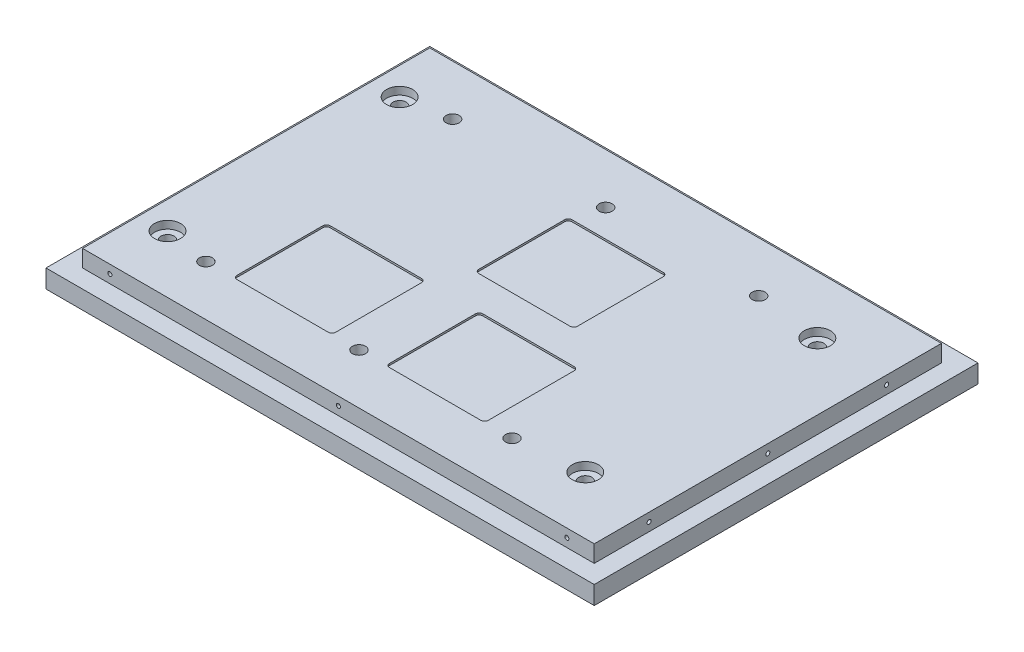
SolidWorks part; units mm, degrees
ref_plane "Front Plane" through (0, 0, 0) normal (0, 0, 1) x (1, 0, 0)
ref_plane "Top Plane" through (0, 0, 0) normal (0, 1, 0) x (1, 0, 0)
ref_plane "Right Plane" through (0, 0, 0) normal (1, 0, 0) x (0, 0, -1)
sketch "Sketch1" plane through (0, 0, 0) normal (0, 1, 0) x (1, 0, 0)
  line L1 (-172.8643, 102.5126) -> (127.1357, 102.5126)
  line L2 (-172.8643, 102.5126) -> (-172.8643, -107.4874)
  line L3 (-172.8643, -107.4874) -> (127.1357, -107.4874)
  line L4 (127.1357, 102.5126) -> (127.1357, -107.4874)
  dimension "D1" = 210
  dimension "D2" = 300
extrude "Boss-Extrude1" add sketch "Sketch1" along normal blind 10
sketch "Sketch2" plane through (0, 10, 0) normal (0, 1, 0) x (1, 0, 0)
  line L0 (-172.8643, 102.5126) -> (-172.8643, -107.4874) construction
  line L1 (-162.8643, 92.5126) -> (117.1357, 92.5126)
  line L2 (-162.8643, 92.5126) -> (-162.8643, -97.4874)
  line L3 (-162.8643, -97.4874) -> (117.1357, -97.4874)
  line L4 (117.1357, 92.5126) -> (117.1357, -97.4874)
  line L5 (127.1357, 102.5126) -> (-172.8643, 102.5126) construction
  line L6 (-172.8643, -107.4874) -> (127.1357, -107.4874) construction
  line L7 (127.1357, -107.4874) -> (127.1357, 102.5126) construction
  dimension "D1" = 10
  dimension "D2" = 10
  dimension "D3" = 10
  dimension "D4" = 10
extrude "Boss-Extrude2" add sketch "Sketch2" along normal blind 9.28
sketch "Sketch3" plane through (0, 19.28, 0) normal (0, 1, 0) x (1, 0, 0)
  line L0 (-162.8643, 92.5126) -> (-162.8643, -97.4874) construction
  line L1 (-122.8643, 65.0126) -> (44.6357, 65.0126)
  line L2 (-122.8643, 65.0126) -> (-122.8643, -69.9874)
  line L3 (-122.8643, -69.9874) -> (44.6357, -69.9874)
  line L4 (44.6357, 65.0126) -> (44.6357, -69.9874)
  line L5 (-39.1143, 65.0126) -> (-39.1143, -69.9874)
  line L6 (-122.8643, -2.4874) -> (44.6357, -2.4874)
  line L8 (-115.3772, -23.5809) -> (-65.3772, -23.5809)
  line L9 (-115.3772, -23.5809) -> (-115.3772, 26.4191)
  line L10 (-115.3772, 26.4191) -> (-65.3772, 26.4191)
  line L11 (-65.3772, -23.5809) -> (-65.3772, 26.4191)
  line L12 (-18.206, 15.3076) -> (31.794, 15.3076)
  line L13 (-18.206, 15.3076) -> (-18.206, 65.3076)
  line L14 (-18.206, 65.3076) -> (31.794, 65.3076)
  line L15 (31.794, 15.3076) -> (31.794, 65.3076)
  circle A0 centre (-122.8643, 65.0126) radius 3.57
  circle A1 centre (-39.1143, 65.0126) radius 3.57
  circle A2 centre (44.6357, 65.0126) radius 3.57
  circle A3 centre (44.6357, -69.9874) radius 3.57
  circle A4 centre (-39.1143, -69.9874) radius 3.57
  circle A5 centre (-122.8643, -69.9874) radius 3.57
  point P4 (-122.8643, -2.4874)
  point P7 (-162.8643, -2.4874)
  dimension "D5" = 7.14
  dimension "D6" = 7.14
  dimension "D1" = 167.5
  dimension "D2" = 135
  dimension "D3" = 0
  dimension "D4" = 40
  dimension "D7" = 50
  dimension "D8" = 50
  dimension "D9" = 50
  dimension "D10" = 50
extrude "1/4-20 clearance holes" cut sketch "Sketch3" against normal up to next contours A0 | A1 | A2 | A3 | A4 | A5
sketch "Sketch4" plane through (0, 0, 0) normal (0, -1, 0) x (1, 0, 0)
  line L0 (-39.1143, 69.9874) -> (-39.1143, -65.0126)
  line L1 (-122.8643, 69.9874) -> (44.6357, 69.9874)
  line L2 (-122.8643, 69.9874) -> (-122.8643, -65.0126)
  line L3 (-122.8643, -65.0126) -> (44.6357, -65.0126)
  line L4 (44.6357, 69.9874) -> (44.6357, -65.0126)
  line L5 (-122.8643, 2.4874) -> (44.6357, 2.4874)
  circle A0 centre (-122.8643, 69.9874) radius 7.5
  circle A1 centre (-39.1143, 69.9874) radius 7.5
  circle A2 centre (44.6357, 69.9874) radius 7.5
  circle A3 centre (44.6357, -65.0126) radius 7.5
  circle A4 centre (-39.1143, -65.0126) radius 7.5
  circle A5 centre (-122.8643, -65.0126) radius 7.5
  dimension "D1" = 15
  dimension "D2" = 15
extrude "Cut-Extrude2" cut sketch "Sketch4" against normal blind 10 contours A0 | A5 | A4 | A3 | A2 | A1
sketch "Sketch5" plane through (0, 0, 97.4874) normal (0, 0, 1) x (1, 0, 0)
  line L0 (-162.8643, 14.64) -> (117.1357, 14.64)
  line L1 (-162.8643, 19.28) -> (-162.8643, 10) construction
  line L2 (117.1357, 19.28) -> (117.1357, 10) construction
  line L3 (-162.8643, 19.28) -> (117.1357, 19.28) construction
  line L4 (-172.8643, 10) -> (127.1357, 10) construction
  line L5 (-22.8643, 10) -> (-22.8643, 19.28)
  circle A0 centre (-147.8643, 14.64) radius 1.13
  circle A1 centre (-22.8643, 14.64) radius 1.13
  circle A2 centre (102.1357, 14.64) radius 1.13
  dimension "D2" = 2.26
  dimension "D3" = 2.26
  dimension "D1" = 15
extrude "4-40 threaded holes" cut sketch "Sketch5" against normal blind 5 contours A0 | A1 | A2
sketch "Sketch6" plane through (0, 0, -92.5126) normal (0, 0, -1) x (-1, 0, 0)
  line L0 (-117.1357, 14.64) -> (162.8643, 14.64)
  line L1 (-117.1357, 19.28) -> (-117.1357, 10) construction
  line L2 (162.8643, 19.28) -> (162.8643, 10) construction
  line L3 (22.8643, 19.28) -> (22.8643, 10)
  line L4 (-117.1357, 19.28) -> (162.8643, 19.28) construction
  line L5 (-127.1357, 10) -> (172.8643, 10) construction
  line L6 (-117.1357, 10) -> (162.8643, 10) construction
  circle A0 centre (-102.1357, 14.64) radius 1.13
  circle A1 centre (22.8643, 14.64) radius 1.13
  circle A2 centre (147.8643, 14.64) radius 1.13
  dimension "D2" = 2.26
  dimension "D3" = 2.26
  dimension "D1" = 15
  dimension "D4" = 250
  dimension "D5" = 4.64
extrude "4-40 threaded holes 2" cut sketch "Sketch6" against normal blind 5 contours A0 | A1 | A2
sketch "Sketch7" plane through (-162.8643, 0, 0) normal (-1, 0, 0) x (0, 0, 1)
  line L0 (-92.5126, 14.64) -> (97.4874, 14.64)
  line L1 (-92.5126, 19.28) -> (-92.5126, 10) construction
  line L2 (97.4874, 19.28) -> (97.4874, 10) construction
  line L3 (2.4874, 19.28) -> (2.4874, 10)
  line L4 (-92.5126, 19.28) -> (97.4874, 19.28) construction
  line L5 (-92.5126, 10) -> (97.4874, 10) construction
  circle A0 centre (-62.5126, 14.64) radius 1.13
  circle A1 centre (2.4874, 14.64) radius 1.13
  circle A2 centre (67.4874, 14.64) radius 1.13
  dimension "D1" = 2.26
  dimension "D2" = 2.26
  dimension "D3" = 130
extrude "4-40 threaded holes 3" cut sketch "Sketch7" against normal blind 5 contours A0 | A1 | A2
sketch "Sketch8" plane through (117.1357, 0, 0) normal (1, 0, 0) x (0, 0, -1)
  line L0 (-97.4874, 14.64) -> (92.5126, 14.64)
  line L1 (-97.4874, 19.28) -> (-97.4874, 10) construction
  line L2 (92.5126, 19.28) -> (92.5126, 10) construction
  line L4 (-97.4874, 19.28) -> (92.5126, 19.28) construction
  line L5 (-2.4874, 19.28) -> (-2.4874, 10)
  line L6 (-107.4874, 10) -> (102.5126, 10) construction
  circle A0 centre (-67.4874, 14.64) radius 1.13
  circle A1 centre (-2.4874, 14.64) radius 1.13
  circle A2 centre (62.5126, 14.64) radius 1.13
  dimension "D1" = 2.26
  dimension "D3" = 2.26
  dimension "D2" = 130
extrude "4-40 threaded holes 4" cut sketch "Sketch8" against normal blind 5 contours A0 | A1 | A2
sketch "Sketch11" plane through (0, 19.28, 0) normal (0, 1, 0) x (1, 0, 0)
  line L1 (-122.8643, 65.0126) -> (44.6357, 65.0126)
  line L2 (-122.8643, 65.0126) -> (-122.8643, -69.9874)
  line L3 (-122.8643, -69.9874) -> (44.6357, -69.9874)
  line L4 (44.6357, 65.0126) -> (44.6357, -69.9874)
  line L5 (-107.8643, -69.9874) -> (-53.8643, -69.9874)
  line L6 (-107.8643, -69.9874) -> (-107.8643, -18.9874)
  line L7 (-107.8643, -18.9874) -> (-53.8643, -18.9874)
  line L8 (-53.8643, -69.9874) -> (-53.8643, -18.9874)
  line L9 (-24.3643, -69.9874) -> (29.6357, -69.9874)
  line L10 (-24.3643, -69.9874) -> (-24.3643, -18.9874)
  line L11 (-24.3643, -18.9874) -> (29.6357, -18.9874)
  line L12 (29.6357, -69.9874) -> (29.6357, -18.9874)
  line L13 (-44.5633, 50.0126) -> (9.4367, 50.0126)
  line L14 (-44.5633, 50.0126) -> (-44.5633, -0.9874)
  line L15 (-44.5633, -0.9874) -> (9.4367, -0.9874)
  line L16 (9.4367, 50.0126) -> (9.4367, -0.9874)
  dimension "D1" = 51
  dimension "D2" = 15
  dimension "D3" = 54
  dimension "D4" = 54
  dimension "D5" = 54
  dimension "D6" = 15
  dimension "D7" = 15
  dimension "D8" = 51
  dimension "D9" = 51
extrude "TEC" cut sketch "Sketch11" against normal blind 1 contours L16 L13 L14 L15 | L3 L8 L7 L6 | L3 L12 L11 L10
fillet "Fillet1" radius 2 12 edges at (9.4367, 18.78, -50.0126) (-44.5633, 18.78, -50.0126) (-44.5633, 18.78, 0.9874) (9.4367, 18.78, 0.9874) (29.6357, 18.78, 18.9874) (29.6357, 18.78, 69.9874) (-24.3643, 18.78, 18.9874) (-24.3643, 18.78, 69.9874) (-107.8643, 18.78, 69.9874) (-53.8643, 18.78, 69.9874) (-53.8643, 18.78, 18.9874) (-107.8643, 18.78, 18.9874)
sketch "Sketch12" plane through (0, 19.28, 0) normal (0, 1, 0) x (1, 0, 0)
  line L0 (-162.8643, 92.5126) -> (-162.8643, -97.4874) construction
  line L1 (-147.8643, 61.0126) -> (80.7357, 61.0126)
  line L2 (-147.8643, 61.0126) -> (-147.8643, -65.9874)
  line L3 (-147.8643, -65.9874) -> (80.7357, -65.9874)
  line L4 (80.7357, 61.0126) -> (80.7357, -65.9874)
  point P6 (-147.8643, -2.4874)
  point P7 (-162.8643, -2.4874)
  dimension "D1" = 228.6
  dimension "D2" = 15
  dimension "D3" = 0
  dimension "D4" = 127
hole_wizard "optical table CBORE for 1/4 Binding Head Machine Screw1" positions "Sketch13" profile "Sketch14" counterbore size "1/4" standard "ANSI Inch" end condition up to next
sketch "Sketch13" plane through (0, 19.28, 0) normal (0, 1, 0) x (1, 0, 0)
  point P0 (-147.8643, 61.0126)
  point P3 (-147.8643, -65.9874)
  point P6 (80.7357, -65.9874)
  point P9 (80.7357, 61.0126)
sketch "Sketch14" plane through (-147.8643, 19.28, -61.0126) normal (1, 0, 0) x (0, 0, 1)
  line L0 (0, 0) -> (0, 19.28)
  line L1 (0, 19.28) -> (3.5712, 19.28)
  line L3 (3.5712, 19.28) -> (3.5712, 4.191)
  line L4 (3.5712, 4.191) -> (7.1437, 4.191)
  line L5 (7.1437, 4.191) -> (7.1437, 0)
  line L7 (7.1437, 0) -> (0, 0)
  line L11 (0, -6.35) -> (0, 107.95) construction
  dimension "Thru Hole Dia." = 7.1425
  dimension "Thru Hole Depth" = 19.28
  dimension "C'Bore Dia." = 14.2875
  dimension "C'Bore Depth" = 4.191
